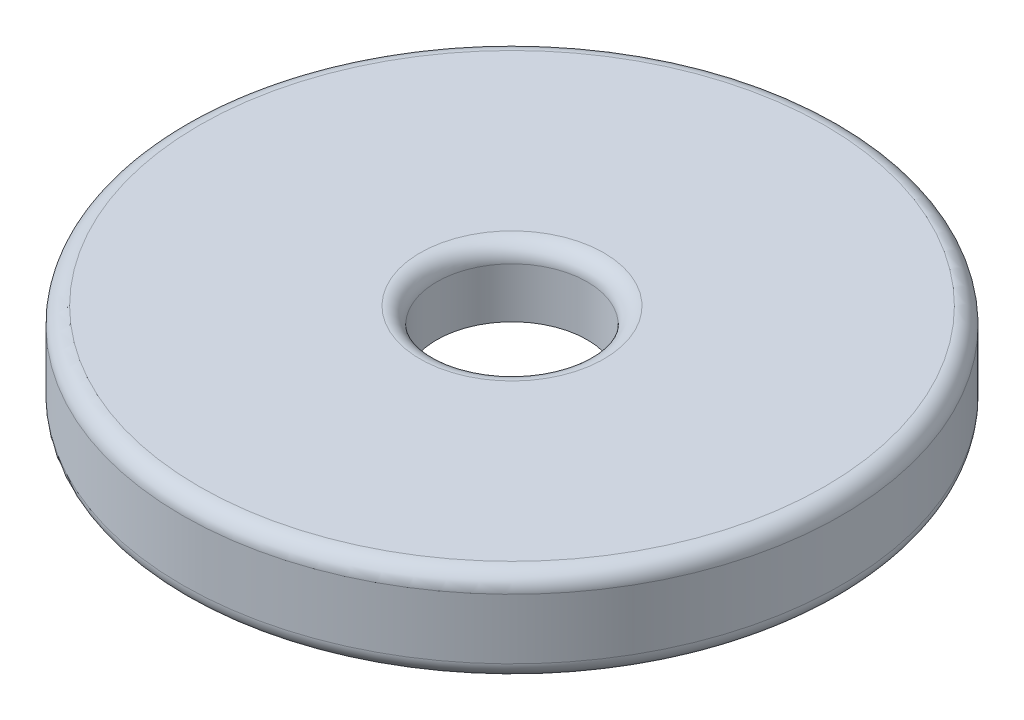
SolidWorks part; units mm, degrees
ref_plane "Front Plane" through (0, 0, 0) normal (0, 0, 1) x (1, 0, 0)
ref_plane "Top Plane" through (0, 0, 0) normal (0, 1, 0) x (1, 0, 0)
ref_plane "Right Plane" through (0, 0, 0) normal (1, 0, 0) x (0, 0, -1)
sketch "Sketch1" plane through (0, 0, 0) normal (0, 0, 1) x (1, 0, 0)
  line L0 (0, 0) -> (-2.2479, 0) construction
  line L1 (-2.2479, 0) -> (-2.2479, 2)
  line L2 (-2.2479, 2) -> (-9.8479, 2)
  line L3 (-9.8479, 2) -> (-9.8479, -0.8)
  line L4 (-9.8479, -0.8) -> (-8.3479, -0.8)
  line L5 (-8.3479, -0.8) -> (-8.3479, 0)
  line L6 (-8.3479, 0) -> (-2.2479, 0)
  line L7 (0, 0) -> (0, 1.6957) construction
  point P7 (-2.2479, 1)
  dimension "D1" = 2.2479
  dimension "D2" = 2
  dimension "D3" = 0.8
  dimension "D4" = 6.1
  dimension "D5" = 1.5
revolve "Revolve1" add sketch "Sketch1" angle 360 about L7
fillet "Fillet1" radius 0.5 4 edges at (0, 2, -9.8479) (0, 2, -2.2479) (0, -0.8, -9.8479) (0, -0.8, -8.3479)
